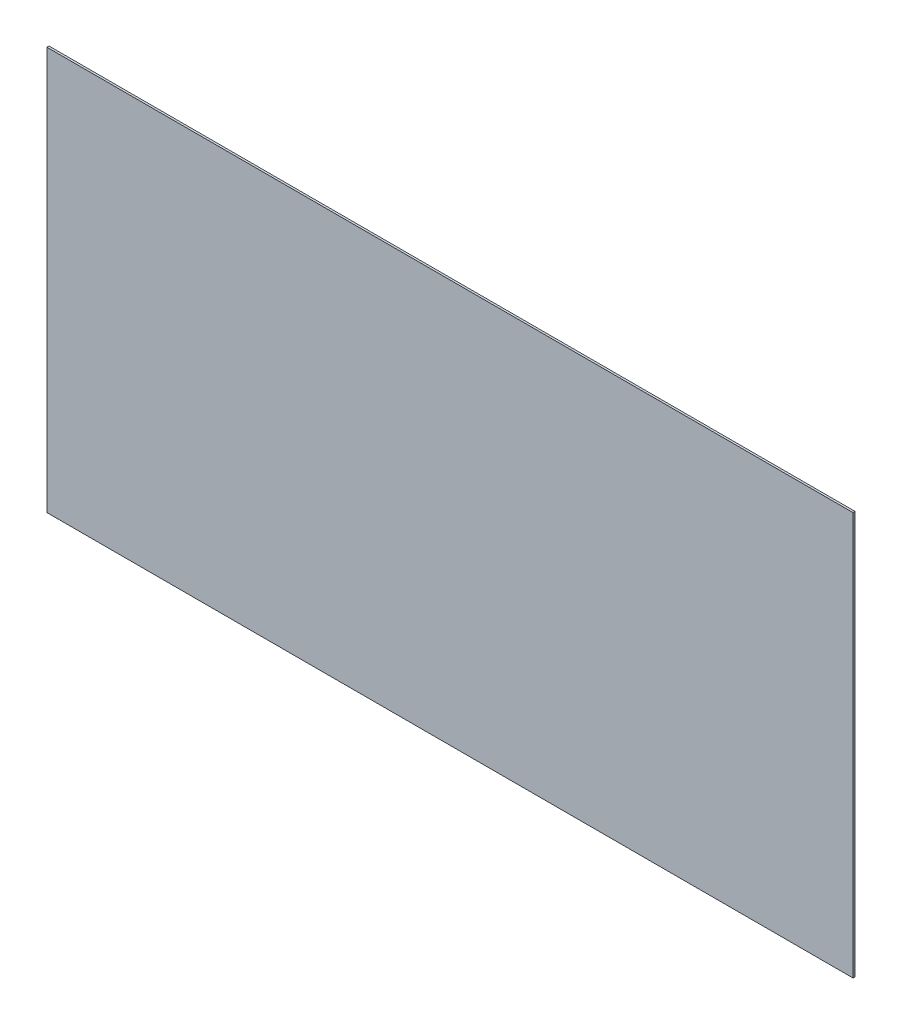
SolidWorks part; units mm, degrees
ref_plane "Front Plane" through (0, 0, 0) normal (0, 0, 1) x (1, 0, 0)
ref_plane "Top Plane" through (0, 0, 0) normal (0, 1, 0) x (1, 0, 0)
ref_plane "Right Plane" through (0, 0, 0) normal (1, 0, 0) x (0, 0, -1)
sketch "Sketch1" plane through (0, 0, 0) normal (0, 0, 1) x (1, 0, 0)
  line L1 (-1219.2, -609.6) -> (1219.2, -609.6)
  line L2 (-1219.2, -609.6) -> (-1219.2, 609.6)
  line L3 (-1219.2, 609.6) -> (1219.2, 609.6)
  line L4 (1219.2, -609.6) -> (1219.2, 609.6)
  line L5 (0, 609.6) -> (0, -609.6) construction
  line L6 (-1219.2, 0) -> (1219.2, 0) construction
  point P0 (0, 0)
  point P4 (-762, 0)
  point P5 (762, 0)
  point P6 (0, 426.72)
  point P7 (0, -426.72)
  dimension "Length" = 2438.4
  dimension "Width" = 1219.2
  dimension "Break" = 457.2
  dimension "D2" = 457.2
  dimension "D1" = 182.88
  dimension "D3" = 182.88
sketch "Sketch2" plane through (0, 0, 0) normal (1, 0, 0) x (0, 0, -1)
  line L0 (-3.175, -609.6) -> (3.175, -609.6)
  dimension "Thickness" = 6.35
sketch "Sketch3" plane through (0, 0, 0) normal (0, 0, 1) x (1, 0, 0)
  line L0 (-1219.2, -609.6) -> (-1219.2, 609.6) construction
  line L1 (-1219.2, -609.6) -> (1219.2, -609.6) construction
  line L2 (1219.2, -609.6) -> (1219.2, 609.6) construction
  line L3 (-1219.2, 609.6) -> (1219.2, 609.6) construction
  line L4 (-1219.2, -609.6) -> (-1219.2, 609.6)
  line L5 (-1219.2, -609.6) -> (1219.2, -609.6)
  line L6 (1219.2, -609.6) -> (1219.2, 609.6)
  line L7 (-1219.2, 609.6) -> (1219.2, 609.6)
extrude "Boss-Extrude1" add sketch "Sketch3" along normal mid plane 6.35
equation "\"D1@Boss-Extrude1\"=\"thickness@sketch2\""
equation "\"Break@Sketch1\"=\"Length@Sketch1\" * .1875"
equation "\"D2@Sketch1\" = \"Break@Sketch1\""
equation "\"D1@Sketch1\"=\"Width@Sketch1\"*0.15"
equation "\"D3@Sketch1\"=\"D1@Sketch1\""
